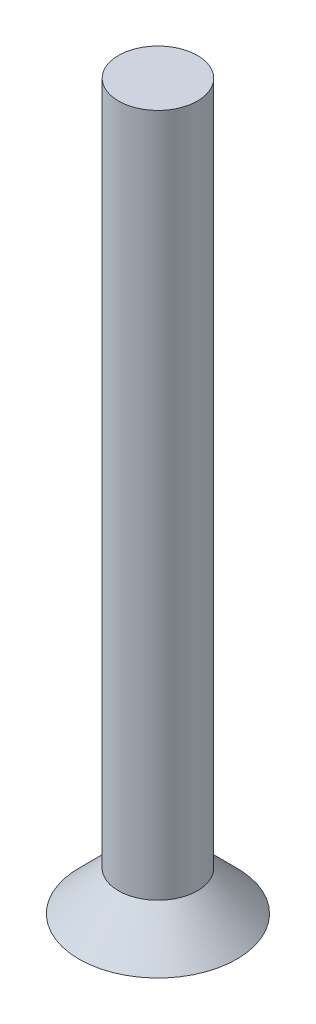
SolidWorks part; units mm, degrees
ref_plane "Plan de face" through (0, 0, 0) normal (0, 0, 1) x (1, 0, 0)
ref_plane "Plan de dessus" through (0, 0, 0) normal (0, 1, 0) x (1, 0, 0)
ref_plane "Plan de droite" through (0, 0, 0) normal (1, 0, 0) x (0, 0, -1)
sketch "Esquisse1" plane through (0, 0, 0) normal (0, 0, 1) x (1, 0, 0)
  line L1 (3, 40) -> (3, -12)
  line L2 (6, -15) -> (3, -12)
  line L3 (6, -15) -> (0, -15)
  line L4 (0, 0) -> (0, -18) construction
  line L5 (0, 40) -> (0, -15)
  line L6 (0, 40) -> (3, 40)
revolve "Révolution1" add sketch "Esquisse1" angle 360 about L4
